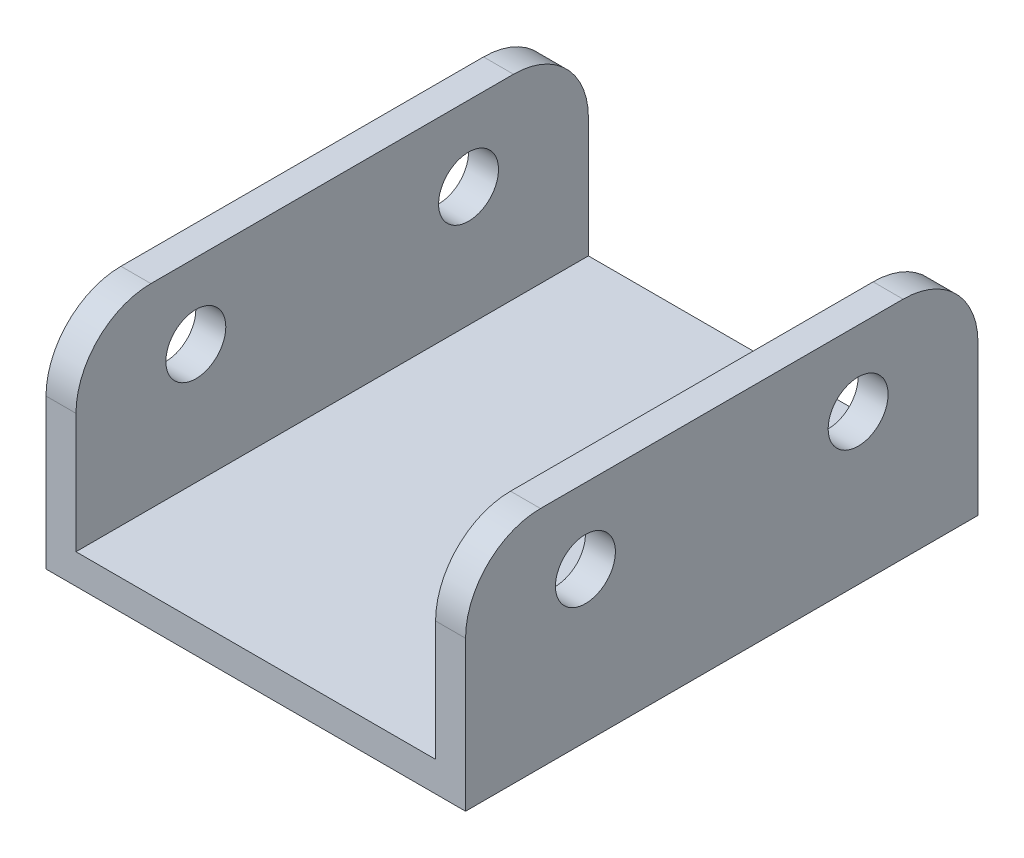
SolidWorks part; units mm, degrees
ref_plane "Front Plane" through (0, 0, 0) normal (0, 0, 1) x (1, 0, 0)
ref_plane "Top Plane" through (0, 0, 0) normal (0, 1, 0) x (1, 0, 0)
ref_plane "Right Plane" through (0, 0, 0) normal (1, 0, 0) x (0, 0, -1)
sketch "Sketch1" plane through (0, 0, 0) normal (0, 0, 1) x (1, 0, 0)
  line L0 (-14, 14) -> (-12, 14)
  line L1 (-12, 14) -> (-12, 1)
  line L2 (-12, 1) -> (12, 1)
  line L3 (14, -1) -> (-14, -1)
  line L4 (-14, -1) -> (-14, 14)
  line L5 (-14, 9) -> (0, 9) construction
  line L6 (0, 1) -> (0, -1) construction
  line L7 (14, 14) -> (12, 14)
  line L8 (14, -1) -> (14, 14)
  line L9 (12, 14) -> (12, 1)
  point P8 (0, 0)
  dimension "D1" = 8
  dimension "D2" = 2
  dimension "D3" = 2
  dimension "D4" = 24
  dimension "D5" = 5
extrude "Boss-Extrude1" add sketch "Sketch1" along normal mid plane 34.2
sketch "Sketch2" plane through (14, 0, 0) normal (1, 0, 0) x (0, 0, -1)
  line L0 (-17.1, -1) -> (-17.1, 14) construction
  line L1 (-17.1, 14) -> (17.1, 14) construction
  line L2 (0, 8.25) -> (0, -8.25) construction
  circle A0 centre (-9.1, 9) radius 2
  circle A1 centre (9.1, 9) radius 2
  dimension "D3" = 4
  dimension "D1" = 8
  dimension "D2" = 5
extrude "Cut-Extrude1" cut sketch "Sketch2" against normal through all both and the other way through all
fillet "Fillet1" radius 5 4 edges at (13, 14, -17.1) (-13, 14, -17.1) (-13, 14, 17.1) (13, 14, 17.1)
